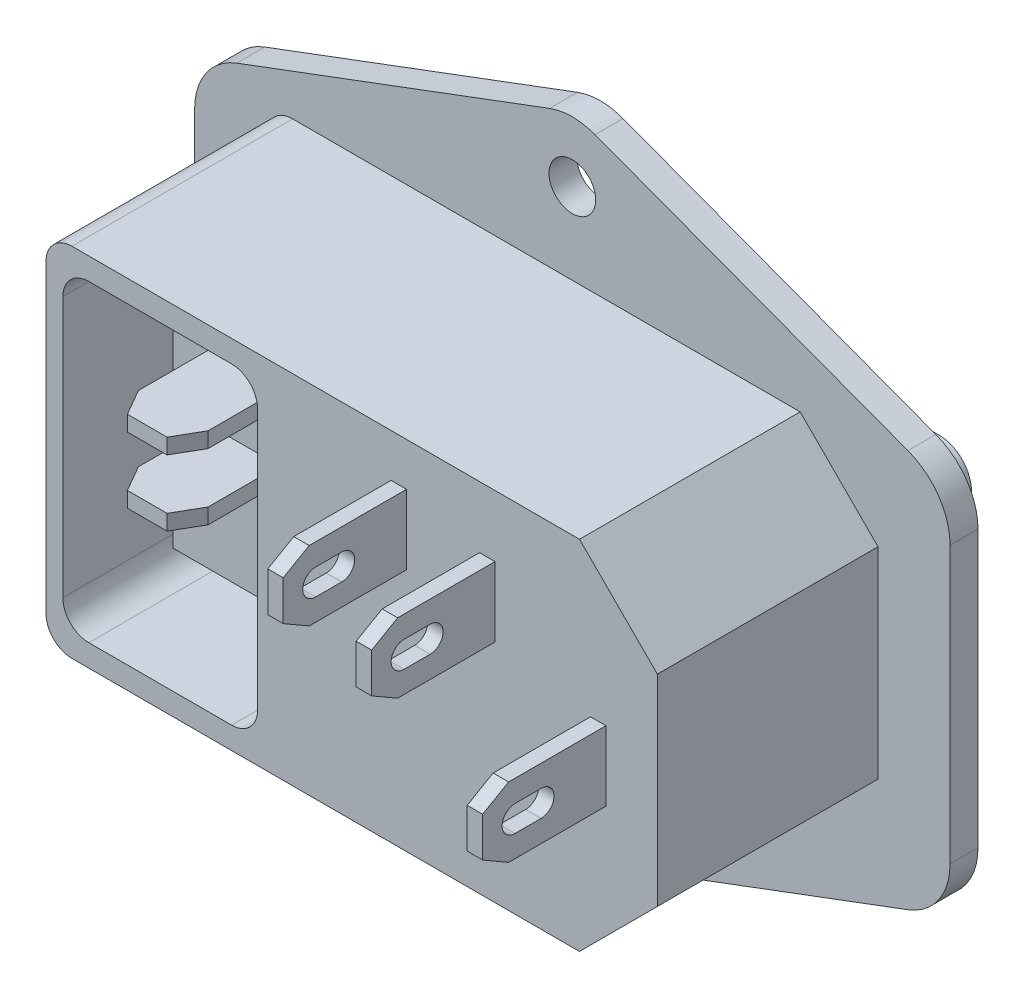
SolidWorks part; units mm, degrees
other "Camera1"
material "ABS"
ref_plane "Front Plane" through (0, 0, 0) normal (0, 0, 1) x (1, 0, 0)
ref_plane "Top Plane" through (0, 0, 0) normal (0, 1, 0) x (1, 0, 0)
ref_plane "Right Plane" through (0, 0, 0) normal (1, 0, 0) x (0, 0, -1)
sketch "Sketch1" plane through (0, 0, 0) normal (0, 0, 1) x (1, 0, 0)
  line L0 (29.1, 0) -> (-29.1, 0) construction
  line L1 (0, 0) -> (0, 20) construction
  line L2 (29.1, -14.1) -> (29.1, 14.1)
  line L3 (29.1, 14.1) -> (0, 25)
  line L4 (29.1, -14.1) -> (0, -25)
  line L5 (29.1, 14.1) -> (0, 25)
  line L6 (29.1, -14.1) -> (0, -25)
  line L7 (-29.1, -14.1) -> (0, -25)
  line L8 (-29.1, 14.1) -> (0, 25)
  line L9 (-29.1, -14.1) -> (0, -25)
  line L10 (-29.1, 14.1) -> (0, 25)
  line L11 (-29.1, -14.1) -> (-29.1, 14.1)
  circle A0 centre (0, 20) radius 1.8
  circle A1 centre (0, -20) radius 1.8
  dimension "D1" = 3.6
  dimension "D2" = 58.2
  dimension "D3" = 28.2
  dimension "D4" = 50
  dimension "D5" = 40
extrude "Boss-Extrude1" add sketch "Sketch1" along normal blind 2.15 contours L11 L7 L4 L2 L3 L8 A0
sketch "Sketch2" plane through (0, 0, 2.15) normal (0, 0, 1) x (1, 0, 0)
  line L1 (23.55, -13.75) -> (-23.55, -13.75)
  line L2 (23.55, -13.75) -> (23.55, 13.75)
  line L3 (23.55, 13.75) -> (-23.55, 13.75)
  line L4 (-23.55, -13.75) -> (-23.55, 13.75)
  line L5 (0, 13.75) -> (0, -13.75) construction
  line L6 (23.55, 0) -> (-23.55, 0) construction
  point P0 (0, 0)
  dimension "D1" = 27.5
  dimension "D2" = 47.1
extrude "Boss-Extrude2" add sketch "Sketch2" along normal blind 17
chamfer "Chamfer1" distance 6 angle 45 2 edges at (23.55, -13.75, 10.65) (23.55, 13.75, 10.65)
fillet "Fillet1" radius 2 2 edges at (-23.55, -13.75, 10.65) (-23.55, 13.75, 10.65)
fillet "Fillet2" radius 5 6 edges at (-29.1, -14.1, 1.075) (-29.1, 14.1, 1.075) (29.1, -14.1, 1.075) (29.1, 14.1, 1.075) (0, -25, 1.075) (0, 25, 1.075)
sketch "Sketch3" plane through (0, 0, 0) normal (0, 0, -1) x (-1, 0, 0)
  line L0 (0, 0) -> (-14.2, 0) construction
  line L1 (-29.1, -10.6336) -> (-29.1, 10.6336) construction
  line L2 (-16.2, -12.1) -> (-6.2, -12.1)
  line L3 (-22.2, -6.1) -> (-22.2, 6.1)
  line L4 (-16.2, 12.1) -> (-6.2, 12.1)
  line L5 (-6.2, -12.1) -> (-6.2, 12.1)
  line L6 (-14.2, 12.1) -> (-14.2, -12.1) construction
  line L7 (-22.2, 0) -> (-6.2, 0) construction
  line L8 (-22.2, 6.1) -> (-16.2, 12.1)
  line L9 (-22.2, -6.1) -> (-16.2, -12.1)
  line L10 (-13.7592, -8.3777) -> (-9.4707, -8.3777)
  line L11 (-19.9662, -0.9293) -> (-15.6778, -0.9293)
  line L12 (-19.9662, -0.9293) -> (-19.9662, 0.9293)
  line L13 (-19.9662, 0.9293) -> (-15.6778, 0.9293)
  line L14 (-15.6778, -0.9293) -> (-15.6778, 0.9293)
  line L15 (-17.822, 0.9293) -> (-17.822, -0.9293) construction
  line L16 (-19.9662, 0) -> (-15.6778, 0) construction
  line L17 (-13.7592, 6.6849) -> (-9.4707, 6.6849)
  line L18 (-13.7592, 6.6849) -> (-13.7592, 8.3777)
  line L19 (-13.7592, 8.3777) -> (-9.4707, 8.3777)
  line L20 (-9.4707, 6.6849) -> (-9.4707, 8.3777)
  line L21 (-11.615, 8.3777) -> (-11.615, 6.6849) construction
  line L22 (-13.7592, 7.5313) -> (-9.4707, 7.5313) construction
  line L23 (-9.4707, -6.6849) -> (-9.4707, -8.3777)
  line L24 (-13.7592, -6.6849) -> (-9.4707, -6.6849)
  line L25 (-13.7592, -6.6849) -> (-13.7592, -8.3777)
  point P4 (-22.2, -12.1)
  point P5 (-22.2, 12.1)
  point P8 (-17.822, 0)
  point P16 (-11.615, 7.5313)
  dimension "D1" = 6.9
  dimension "D2" = 16
  dimension "D3" = 24.2
extrude "Cut-Extrude1" cut sketch "Sketch3" against normal blind 17
sketch "Sketch4" plane through (0, 0, 0) normal (0, 0, -1) x (-1, 0, 0)
  line L0 (-6.2, -12.1) -> (-6.2, 12.1) construction
  line L1 (-24.7, -14) -> (24.7, -14)
  line L2 (-27.2, -11.5) -> (-27.2, 11.5)
  line L3 (-24.7, 14) -> (24.7, 14)
  line L4 (27.2, -11.5) -> (27.2, 11.5)
  line L5 (0, 14) -> (0, -14) construction
  line L6 (-27.2, 0) -> (27.2, 0) construction
  line L7 (-16.2, -12.1) -> (-6.2, -12.1) construction
  line L8 (-22.2, -6.1) -> (-16.2, -12.1) construction
  line L9 (-22.2, 6.1) -> (-22.2, -6.1) construction
  line L10 (-16.2, 12.1) -> (-22.2, 6.1) construction
  line L11 (-6.2, 12.1) -> (-16.2, 12.1) construction
  line L12 (-6.2, -12.1) -> (-6.2, 12.1)
  line L13 (-16.2, -12.1) -> (-6.2, -12.1)
  line L14 (-22.2, -6.1) -> (-16.2, -12.1)
  line L15 (-22.2, 6.1) -> (-22.2, -6.1)
  line L16 (-16.2, 12.1) -> (-22.2, 6.1)
  line L17 (-6.2, 12.1) -> (-16.2, 12.1)
  arc A0 (24.7, 14) -> (27.2, 11.5) centre (24.7, 11.5) cw
  arc A1 (24.7, -14) -> (27.2, -11.5) centre (24.7, -11.5) ccw
  arc A2 (-24.7, -14) -> (-27.2, -11.5) centre (-24.7, -11.5) cw
  arc A3 (-27.2, 11.5) -> (-24.7, 14) centre (-24.7, 11.5) cw
  point P0 (0, 0)
  point P11 (27.2, 14)
  point P15 (27.2, -14)
  point P21 (-27.2, 14)
  dimension "D3" = 2.5
  dimension "D1" = 54.4
  dimension "D2" = 28
extrude "Boss-Extrude3" add sketch "Sketch4" along normal blind 1.4
sketch "Sketch5" plane through (0, 0, -1.4) normal (0, 0, -1) x (-1, 0, 0)
  line L0 (5.4, 0) -> (0, 0) construction
  line L1 (-3.1, 12.25) -> (5.4, 12.25)
  line L2 (-3.1, 12.25) -> (-3.1, -12.25)
  line L3 (-3.1, -12.25) -> (5.4, -12.25)
  line L4 (5.4, 12.25) -> (5.4, -12.25)
  line L5 (-3.3, 12.45) -> (-3.3, -12.45)
  line L6 (-3.3, -12.45) -> (5.6, -12.45)
  line L7 (5.6, 12.45) -> (5.6, -12.45)
  line L8 (-3.3, 12.45) -> (5.6, 12.45)
  line L9 (2.6883, 5.0513) -> (4.1482, 5.0513)
  line L10 (-1.3893, 9.1406) -> (4.1482, 9.1406)
  line L11 (-1.3893, 9.1406) -> (-1.3893, 5.0513)
  line L12 (-1.3893, 5.0513) -> (0.0706, 5.0513)
  line L13 (4.1482, 9.1406) -> (4.1482, 5.0513)
  line L15 (0.0706, 5.0513) -> (0.0706, -5.0513)
  line L16 (0.0706, 0) -> (2.6883, 0)
  line L17 (2.6883, 5.0513) -> (2.6883, -5.0513)
  line L18 (-1.3893, -9.1406) -> (4.1482, -9.1406)
  line L19 (-1.3893, -9.1406) -> (-1.3893, -5.0513)
  line L20 (-1.3893, -5.0513) -> (0.0706, -5.0513)
  line L21 (2.6883, -5.0513) -> (4.1482, -5.0513)
  line L22 (4.1482, -9.1406) -> (4.1482, -5.0513)
  line L23 (-1.6893, -9.4406) -> (4.4482, -9.4406)
  line L24 (4.4482, -9.4406) -> (4.4482, -4.7513)
  line L25 (2.9883, -4.7513) -> (4.4482, -4.7513)
  line L26 (2.9883, 4.7513) -> (2.9883, -4.7513)
  line L27 (2.9883, 4.7513) -> (4.4482, 4.7513)
  line L28 (4.4482, 9.4406) -> (4.4482, 4.7513)
  line L29 (-1.6893, 9.4406) -> (4.4482, 9.4406)
  line L30 (-1.6893, 9.4406) -> (-1.6893, 4.7513)
  line L31 (-1.6893, 4.7513) -> (-0.2294, 4.7513)
  line L32 (-0.2294, 4.7513) -> (-0.2294, -4.7513)
  line L33 (-1.6893, -4.7513) -> (-0.2294, -4.7513)
  line L34 (-1.6893, -9.4406) -> (-1.6893, -4.7513)
  line L35 (-29.1, -10.6336) -> (-29.1, 10.6336) construction
  line L36 (1.3795, 9.1406) -> (1.3795, -9.1406) construction
  dimension "D2" = 24.5
  dimension "D3" = 8.5
  dimension "D5" = 25.8
  dimension "D1" = 0.2
  dimension "D4" = 0.3
extrude "Cut-Extrude2" cut sketch "Sketch5" against normal blind 0.2 contours L8 L5 L6 L7 L1 L4 L3 L2 | L0 L26 L27 L28 L29 L30 L31 L32 L15 L12 L11 L10 L13 L9 L17 | L26 L0 L17 L21 L22 L18 L19 L20 L15 L32 L33 L34 L23 L24 L25
sketch "Sketch6" plane through (0, 0, -1.4) normal (0, 0, -1) x (-1, 0, 0)
  line L0 (0, 0) -> (14.75, 0) construction
  line L2 (9.25, -12.05) -> (20.25, -12.05)
  line L3 (7.25, -10.05) -> (7.25, 10.05)
  line L4 (9.25, 12.05) -> (20.25, 12.05)
  line L5 (22.25, -10.05) -> (22.25, 10.05)
  line L6 (14.75, 12.05) -> (14.75, -12.05) construction
  line L7 (7.25, 0) -> (22.25, 0) construction
  line L8 (23.55, 11.75) -> (23.55, -11.75) construction
  arc A0 (20.25, -12.05) -> (22.25, -10.05) centre (20.25, -10.05) ccw
  arc A1 (9.25, -12.05) -> (7.25, -10.05) centre (9.25, -10.05) cw
  arc A2 (7.25, 10.05) -> (9.25, 12.05) centre (9.25, 10.05) cw
  arc A3 (20.25, 12.05) -> (22.25, 10.05) centre (20.25, 10.05) cw
  point P10 (22.25, -12.05)
  point P16 (7.25, 12.05)
  point P19 (22.25, 12.05)
  dimension "D4" = 2
  dimension "D1" = 24.1
  dimension "D2" = 1.3
  dimension "D3" = 15
extrude "Cut-Extrude3" cut sketch "Sketch6" along normal blind 17.7 from surface at -20.55 starting at face at (-1.1036, 0, 19.15)
sketch "Sketch8" plane through (0, 0, 1.45) normal (0, 0, 1) x (1, 0, 0)
  line L0 (-7.25, 0) -> (-22.25, 0) construction
  line L1 (-7.25, -10.05) -> (-7.25, 10.05) construction
  line L2 (-22.25, 10.05) -> (-22.25, -10.05) construction
  line L4 (-20.25, -9) -> (-9.25, -9)
  line L5 (-20.25, -9) -> (-20.25, 9)
  line L6 (-20.25, 9) -> (-9.25, 9)
  line L7 (-9.25, -9) -> (-9.25, 9)
  line L8 (-14.75, 9) -> (-14.75, -9) construction
  line L9 (-20.25, 0) -> (-9.25, 0) construction
  point P6 (-14.75, 0)
  dimension "D1" = 11
  dimension "D2" = 18
extrude "Boss-Extrude4" add sketch "Sketch8" along normal blind 11.2
sketch "Sketch9" plane through (0, 0, 12.65) normal (0, 0, 1) x (1, 0, 0)
  line L0 (-14.75, 9) -> (-14.75, -9) construction
  line L1 (-9.25, 9) -> (-20.25, 9) construction
  line L2 (-20.25, -9) -> (-9.25, -9) construction
  line L4 (-17.4335, 4.4885) -> (-12.0665, 4.4885)
  line L5 (-17.4335, 4.4885) -> (-17.4335, 5.6786)
  line L6 (-17.4335, 5.6786) -> (-12.0665, 5.6786)
  line L7 (-12.0665, 4.4885) -> (-12.0665, 5.6786)
  line L8 (-14.75, 5.6786) -> (-14.75, 4.4885) construction
  line L9 (-17.4335, 5.0835) -> (-12.0665, 5.0835) construction
  line L10 (-17.4335, -0.595) -> (-12.0665, -0.595)
  line L11 (-17.4335, -0.595) -> (-17.4335, 0.595)
  line L12 (-17.4335, 0.595) -> (-12.0665, 0.595)
  line L13 (-12.0665, -0.595) -> (-12.0665, 0.595)
  line L14 (-14.75, 0.595) -> (-14.75, -0.595) construction
  line L15 (-17.4335, 0) -> (-12.0665, 0) construction
  point P6 (-14.75, 5.0835)
  point P10 (-14.75, 0)
extrude "Boss-Extrude5" add sketch "Sketch9" along normal blind 7.5
sketch "Sketch10" plane through (0, 0, -1.4) normal (0, 0, -1) x (-1, 0, 0)
  line L0 (20.25, 0) -> (9.25, 0) construction
  line L1 (20.25, 9) -> (20.25, -9) construction
  line L2 (9.25, -9) -> (9.25, 9) construction
  line L4 (7.075, -10.775) -> (22.425, -10.775)
  line L5 (7.075, -10.775) -> (7.075, 10.775)
  line L6 (7.075, 10.775) -> (22.425, 10.775)
  line L7 (22.425, -10.775) -> (22.425, 10.775)
  line L8 (14.75, 10.775) -> (14.75, -10.775) construction
  line L9 (7.075, 0) -> (22.425, 0) construction
  point P6 (14.75, 0)
  dimension "D1" = 15.35
  dimension "D2" = 21.55
extrude "Cut-Extrude4" cut sketch "Sketch10" against normal blind 1.5
sketch "Sketch12" plane through (0, 0, 0.1) normal (0, 0, -1) x (-1, 0, 0)
  line L0 (22.425, 0) -> (7.075, 0) construction
  line L1 (22.425, -10.775) -> (22.425, 10.775) construction
  line L2 (7.075, 10.775) -> (7.075, -10.775) construction
  line L3 (22.425, 10.775) -> (7.075, 10.775) construction
  line L4 (7.175, -10.675) -> (22.325, -10.675)
  line L5 (7.175, -10.675) -> (7.175, 10.675)
  line L6 (7.175, 10.675) -> (22.325, 10.675)
  line L7 (22.325, -10.675) -> (22.325, 10.675)
  line L8 (14.75, 10.675) -> (14.75, -10.675) construction
  line L9 (7.175, 0) -> (22.325, 0) construction
  line L10 (9.675, 8.175) -> (19.825, 8.175)
  line L11 (19.825, -8.175) -> (19.825, 8.175)
  line L12 (9.675, -8.175) -> (19.825, -8.175)
  line L13 (9.675, -8.175) -> (9.675, 8.175)
  point P6 (14.75, 0)
  dimension "D1" = 0.1
  dimension "D2" = 0.1
  dimension "D3" = 2.5
extrude "Boss-Extrude6" add sketch "Sketch12" along normal blind 1.5
ref_plane "Plane2" through (-14.75, 0, 0) normal (1, 0, 0) x (0, 0, -1)
sketch "Sketch13" plane through (-14.75, 0, 0) normal (1, 0, 0) x (0, 0, -1)
  line L0 (-0.1, -7.4254) -> (-0.1, 7.5928)
  line L1 (-0.1, -8.175) -> (-0.1, 8.175) construction
  line L2 (-0.1, -10.675) -> (-0.1, 10.675) construction
  line L3 (-0.1, -7.4254) -> (1.4, -7.4254)
  line L4 (1.4, -8.175) -> (1.4, 8.175) construction
  spline S0 degree 2 poles (-0.1, 7.5928) (3.6595, 7.4366) (6.7405, 5.1709) knots 0 0 0 1 1 1
  spline S1 degree 2 poles (1.4, -7.4254) (1.3492, 0.0577) (6.7405, 5.1709) knots 0 0 0 1 1 1
extrude "Boss-Extrude7" add sketch "Sketch13" along normal mid plane 10
sketch "Sketch14" plane through (0, 0, 19.15) normal (0, 0, 1) x (1, 0, 0)
  line L0 (0, 0) -> (-31.6043, 0) construction
  line L1 (-12.0665, 4.4885) -> (-12.0665, 5.6786) construction
  line L6 (-17.4335, 4.4885) -> (-12.0665, 4.4885) construction
  line L8 (4.2266, 10.4223) -> (3.0366, 10.4223)
  line L9 (4.2266, 10.4223) -> (4.2266, 5.0553)
  line L10 (4.2266, 5.0553) -> (3.0366, 5.0553)
  line L11 (3.0366, 10.4223) -> (3.0366, 5.0553)
  line L12 (9.8491, 9.005) -> (11.0392, 9.005)
  line L13 (9.8491, 9.005) -> (9.8491, 3.638)
  line L14 (9.8491, 3.638) -> (11.0392, 3.638)
  line L15 (11.0392, 9.005) -> (11.0392, 3.638)
  line L16 (18.3991, 2.3296) -> (19.5892, 2.3296)
  line L17 (18.3991, 2.3296) -> (18.3991, -3.0374)
  line L18 (18.3991, -3.0374) -> (19.5892, -3.0374)
  line L19 (19.5892, 2.3296) -> (19.5892, -3.0374)
extrude "Boss-Extrude8" add sketch "Sketch14" along normal blind 9.5
chamfer "Chamfer3" distance 1 angle 60 4 edges at (-7.175, 0, -1.4) (-14.75, -10.675, -1.4) (-22.325, 0, -1.4) (-14.75, 10.675, -1.4)
chamfer "Chamfer2" distance 2 angle 30 16 edges at (13.7592, -7.5313, 0) (9.4707, -7.5313, 0) (19.9662, 0, 0) (15.6778, 0, 0) (13.7592, 7.5313, 0) (9.4707, 7.5313, 0) (-17.4335, 5.0835, 20.15) (-12.0665, 5.0835, 20.15) (-12.0665, 0, 20.15) (-17.4335, 0, 20.15) (18.9941, -3.0374, 28.65) (18.9941, 2.3296, 28.65) (10.4441, 9.005, 28.65) (10.4441, 3.638, 28.65) (3.6316, 10.4223, 28.65) (3.6316, 5.0553, 28.65)
sketch "Sketch15" plane through (19.5892, 0, 0) normal (1, 0, 0) x (0, 0, -1)
  line L0 (-28.65, -0.3539) -> (-25.15, -0.3539) construction
  line L1 (-28.65, -1.8827) -> (-28.65, 1.1749) construction
  line L2 (-26.15, -0.3539) -> (-24.15, -0.3539) construction
  line L3 (-26.15, 0.6461) -> (-24.15, 0.6461)
  line L4 (-26.15, -1.3539) -> (-24.15, -1.3539)
  arc A0 (-26.15, 0.6461) -> (-26.15, -1.3539) centre (-26.15, -0.3539) ccw
  arc A1 (-24.15, -1.3539) -> (-24.15, 0.6461) centre (-24.15, -0.3539) ccw
  point P6 (-25.15, -0.3539)
  dimension "D3" = 1
  dimension "D1" = 3.5
  dimension "D2" = 2
extrude "Cut-Extrude5" cut sketch "Sketch15" against normal blind 10
sketch "Sketch16" plane through (11.0392, 0, 0) normal (1, 0, 0) x (0, 0, -1)
  line L0 (-28.65, 6.3215) -> (-25.15, 6.3215) construction
  line L1 (-28.65, 4.7927) -> (-28.65, 7.8503) construction
  line L2 (-24.15, 6.3215) -> (-26.15, 6.3215) construction
  line L3 (-24.15, 5.3215) -> (-26.15, 5.3215)
  line L4 (-24.15, 7.3215) -> (-26.15, 7.3215)
  line L5 (-26.15, 0.6461) -> (-24.15, 0.6461) construction
  arc A0 (-24.15, 5.3215) -> (-24.15, 7.3215) centre (-24.15, 6.3215) ccw
  arc A1 (-26.15, 7.3215) -> (-26.15, 5.3215) centre (-26.15, 6.3215) ccw
  point P8 (-25.15, 6.3215)
  dimension "D1" = 1
extrude "Cut-Extrude6" cut sketch "Sketch16" against normal blind 2
sketch "Sketch17" plane through (3.0366, 0, 0) normal (-1, 0, 0) x (0, 0, 1)
  line L0 (28.65, 7.7388) -> (25.15, 7.7388) construction
  line L1 (28.65, 9.2676) -> (28.65, 6.21) construction
  line L2 (24.15, 7.7388) -> (26.15, 7.7388) construction
  line L3 (24.15, 8.7388) -> (26.15, 8.7388)
  line L4 (24.15, 6.7389) -> (26.15, 6.7389)
  line L5 (26.15, 0.6461) -> (24.15, 0.6461) construction
  arc A0 (24.15, 8.7388) -> (24.15, 6.7389) centre (24.15, 7.7388) ccw
  arc A1 (26.15, 6.7389) -> (26.15, 8.7388) centre (26.15, 7.7388) ccw
  point P7 (25.15, 7.7388)
  dimension "D1" = 1
extrude "Cut-Extrude7" cut sketch "Sketch17" against normal blind 2
